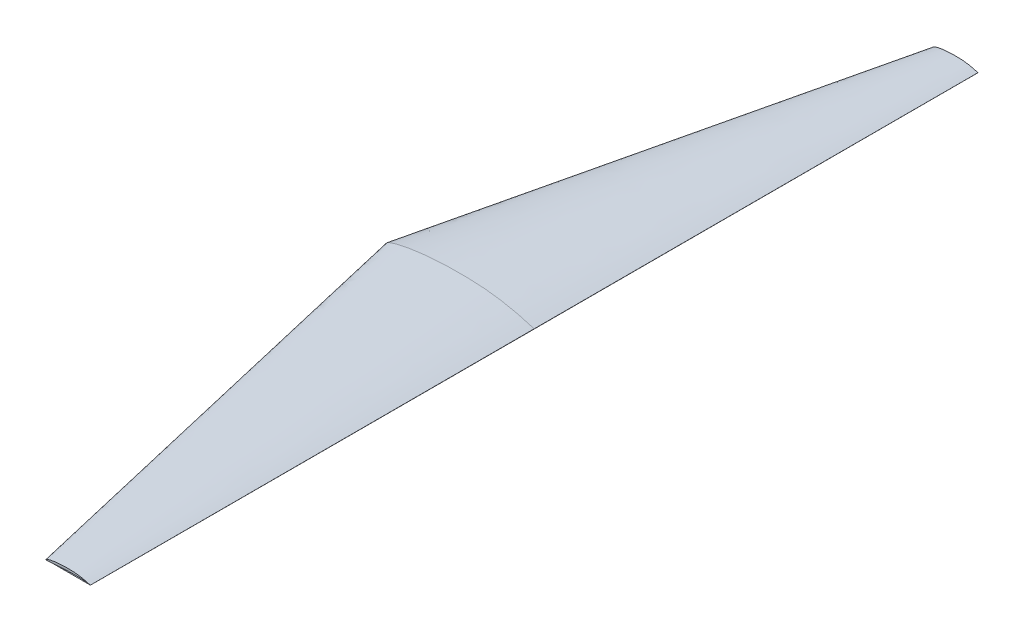
SolidWorks part; units mm, degrees
ref_plane "Front Plane" through (0, 0, 0) normal (0, 0, 1) x (1, 0, 0)
ref_plane "Top Plane" through (0, 0, 0) normal (0, 1, 0) x (1, 0, 0)
ref_plane "Right Plane" through (0, 0, 0) normal (1, 0, 0) x (0, 0, -1)
curve "Curve1"
  spline degree 3 poles (25.4, 0.016, 0) (25.3391, 0.0354, 0) (25.1691, 0.0896, 0) (24.8604, 0.1853, 0) (24.4521, 0.3079, 0) (23.9748, 0.4451, 0) (23.4435, 0.5905, 0) (22.8682, 0.7391, 0) (22.2564, 0.887, 0) (21.6142, 1.0313, 0) (20.9466, 1.1694, 0) (20.258, 1.299, 0) (19.5521, 1.4184, 0) (18.8325, 1.5262, 0) (18.1021, 1.6212, 0) (17.3637, 1.7024, 0) (16.6199, 1.7689, 0) (15.8731, 1.8208, 0) (15.1255, 1.8558, 0) (14.3793, 1.8809, 0) (13.6365, 1.8983, 0) (12.8989, 1.9074, 0) (12.1682, 1.9083, 0) (11.4461, 1.901, 0) (10.7342, 1.8857, 0) (10.0342, 1.8625, 0) (9.3474, 1.8315, 0) (8.6753, 1.7932, 0) (8.0194, 1.7478, 0) (7.3808, 1.6956, 0) (6.761, 1.637, 0) (6.1612, 1.5726, 0) (5.5826, 1.5027, 0) (5.0264, 1.428, 0) (4.4936, 1.3489, 0) (3.9856, 1.2661, 0) (3.5033, 1.1802, 0) (3.0477, 1.0919, 0) (2.6201, 1.0017, 0) (2.2213, 0.9105, 0) (1.8523, 0.8188, 0) (1.5142, 0.7273, 0) (1.2078, 0.6366, 0) (0.9341, 0.5475, 0) (0.694, 0.4605, 0) (0.4882, 0.3763, 0) (0.3176, 0.2954, 0) (0.1826, 0.2183, 0) (0.0836, 0.145, 0) (0.0195, 0.0755, 0) (-0.008, 0.0023, 0) (0.0173, -0.0678, 0) (0.0849, -0.1179, 0) (0.1842, -0.1582, 0) (0.3194, -0.1909, 0) (0.4898, -0.2162, 0) (0.6954, -0.2344, 0) (0.9354, -0.2455, 0) (1.209, -0.2497, 0) (1.5153, -0.2472, 0) (1.8533, -0.2383, 0) (2.2222, -0.2234, 0) (2.621, -0.2028, 0) (3.0486, -0.1768, 0) (3.504, -0.1458, 0) (3.9863, -0.1104, 0) (4.4943, -0.0708, 0) (5.0269, -0.0277, 0) (5.5831, 0.0186, 0) (6.1617, 0.0673, 0) (6.7614, 0.1181, 0) (7.3812, 0.1704, 0) (8.0196, 0.2236, 0) (8.6755, 0.2771, 0) (9.3475, 0.3304, 0) (10.0343, 0.3829, 0) (10.7343, 0.4341, 0) (11.446, 0.4835, 0) (12.1681, 0.5305, 0) (12.8988, 0.5746, 0) (13.6364, 0.6156, 0) (14.3791, 0.6529, 0) (15.1252, 0.6867, 0) (15.8725, 0.7144, 0) (16.6192, 0.7287, 0) (17.363, 0.7312, 0) (18.1013, 0.7217, 0) (18.8317, 0.7006, 0) (19.5514, 0.6682, 0) (20.2572, 0.6255, 0) (20.9458, 0.5732, 0) (21.6134, 0.5125, 0) (22.2557, 0.4449, 0) (22.8675, 0.3721, 0) (23.4429, 0.2962, 0) (23.9743, 0.2197, 0) (24.4517, 0.1457, 0) (24.8601, 0.0785, 0) (25.1689, 0.0253, 0) (25.3391, -0.0051, 0) (25.4, -0.016, 0) knots 0 0 0 0 0.003729 0.010403 0.018841 0.028586 0.039358 0.050957 0.063231 0.076057 0.089334 0.102977 0.11691 0.131071 0.145402 0.159854 0.17438 0.18894 0.203496 0.218017 0.232469 0.246817 0.261029 0.275074 0.288921 0.302543 0.315913 0.329004 0.341791 0.35425 0.366358 0.37809 0.389424 0.400339 0.410813 0.420824 0.430352 0.439376 0.447877 0.455834 0.463229 0.470043 0.476257 0.481856 0.486823 0.491146 0.494814 0.497827 0.500195 0.50197 0.5033 0.504509 0.506013 0.508063 0.510747 0.514093 0.518105 0.522777 0.528099 0.534057 0.540634 0.547815 0.555582 0.563914 0.572793 0.582198 0.592109 0.602502 0.613357 0.624649 0.636356 0.648452 0.660912 0.673711 0.686822 0.700217 0.713868 0.727745 0.741819 0.756057 0.770426 0.784892 0.799419 0.813968 0.828496 0.842964 0.85733 0.871548 0.885567 0.89933 0.912776 0.925832 0.938415 0.950429 0.961757 0.972255 0.981732 0.989922 0.99639 1 1 1 1
sketch "Sketch3" plane through (0, 0, 0) normal (0, 0, 1) x (1, 0, 0)
  line L0 (25.4, 0.016) -> (25.4, -0.016)
  line L1 (0, 0) -> (25.4, 0) construction
  spline S0 degree 3 poles (976.7021, 2844.8263) (53.073, -21.0739) (40.8374, -4.7691) (24.8604, 0.1853) (24.4521, 0.3079) (23.7837, 0.5001) (22.615, 0.8106) (21.3697, 1.0897) (20.0193, 1.3439) (19.0695, 1.4954) (18.1021, 1.6212) (17.3637, 1.7024) (16.6199, 1.7689) (15.8731, 1.8208) (15.1255, 1.8558) (14.3793, 1.8809) (13.6365, 1.8983) (12.658, 1.9103) (11.6898, 1.9063) (10.505, 1.8807) (9.5807, 1.8449) (8.6753, 1.7932) (8.0194, 1.7478) (7.3808, 1.6956) (6.761, 1.637) (6.1612, 1.5726) (5.5826, 1.5027) (5.0264, 1.428) (4.4936, 1.3489) (3.9856, 1.2661) (3.5033, 1.1802) (3.0477, 1.0919) (2.6201, 1.0017) (2.2213, 0.9105) (1.8523, 0.8188) (1.5142, 0.7273) (1.2078, 0.6366) (0.9341, 0.5475) (0.694, 0.4605) (0.4882, 0.3763) (0.3176, 0.2954) (0.1826, 0.2183) (0.0836, 0.145) (0.0195, 0.0755) (-0.008, 0.0023) (0.0173, -0.0678) (0.0849, -0.1179) (0.1842, -0.1582) (0.3194, -0.1909) (0.4898, -0.2162) (0.6954, -0.2344) (0.9354, -0.2455) (1.209, -0.2497) (1.5153, -0.2472) (1.8533, -0.2383) (2.2222, -0.2234) (2.621, -0.2028) (3.0486, -0.1768) (3.504, -0.1458) (3.9863, -0.1104) (4.4943, -0.0708) (5.0269, -0.0277) (5.5831, 0.0186) (6.1617, 0.0673) (6.7614, 0.1181) (7.3812, 0.1704) (8.0196, 0.2236) (8.6755, 0.2771) (9.5809, 0.3489) (10.7458, 0.4363) (11.9305, 0.5161) (12.8988, 0.5746) (13.6364, 0.6156) (14.3791, 0.6529) (15.1252, 0.6867) (15.8725, 0.7144) (16.6192, 0.7287) (17.363, 0.7312) (18.1013, 0.7217) (19.0677, 0.6937) (20.2411, 0.6319) (21.5894, 0.5195) (22.6536, 0.4003) (23.4429, 0.2962) (23.9743, 0.2197) (24.4517, 0.1457) (24.8601, 0.0785) (42.1529, -2.8996) (57.3926, -16.6778) (598.7349, 2944.3395) knots -0.956465 -0.956465 -0.956465 -0.956465 0.003729 0.010403 0.018841 0.028586 0.050957 0.089334 0.102977 0.131071 0.145402 0.159854 0.17438 0.18894 0.203496 0.218017 0.232469 0.246817 0.275074 0.288921 0.315913 0.329004 0.341791 0.35425 0.366358 0.37809 0.389424 0.400339 0.410813 0.420824 0.430352 0.439376 0.447877 0.455834 0.463229 0.470043 0.476257 0.481856 0.486823 0.491146 0.494814 0.497827 0.500195 0.50197 0.5033 0.504509 0.506013 0.508063 0.510747 0.514093 0.518105 0.522777 0.528099 0.534057 0.540634 0.547815 0.555582 0.563914 0.572793 0.582198 0.592109 0.602502 0.613357 0.624649 0.636356 0.648452 0.660912 0.673711 0.686822 0.713868 0.741819 0.756057 0.770426 0.784892 0.799419 0.813968 0.828496 0.842964 0.85733 0.871548 0.89933 0.925832 0.950429 0.961757 0.972255 0.981732 0.989922 0.99639 2.004842 2.004842 2.004842 2.004842 only from (25.4, 0.016) to (25.4, -0.016) construction
  spline S1 degree 3 poles (25.4, 0.016) (25.3391, 0.0354) (25.1691, 0.0896) (24.8604, 0.1853) (24.4521, 0.3079) (23.7837, 0.5001) (22.615, 0.8106) (21.3697, 1.0897) (20.0193, 1.3439) (19.0695, 1.4954) (18.1021, 1.6212) (17.3637, 1.7024) (16.6199, 1.7689) (15.8731, 1.8208) (15.1255, 1.8558) (14.3793, 1.8809) (13.6365, 1.8983) (12.658, 1.9103) (11.6898, 1.9063) (10.505, 1.8807) (9.5807, 1.8449) (8.6753, 1.7932) (8.0194, 1.7478) (7.3808, 1.6956) (6.761, 1.637) (6.1612, 1.5726) (5.5826, 1.5027) (5.0264, 1.428) (4.4936, 1.3489) (3.9856, 1.2661) (3.5033, 1.1802) (3.0477, 1.0919) (2.6201, 1.0017) (2.2213, 0.9105) (1.8523, 0.8188) (1.5142, 0.7273) (1.2078, 0.6366) (0.9341, 0.5475) (0.694, 0.4605) (0.4882, 0.3763) (0.3176, 0.2954) (0.1826, 0.2183) (0.0836, 0.145) (0.0195, 0.0755) (-0.008, 0.0023) (0.0173, -0.0678) (0.0849, -0.1179) (0.1842, -0.1582) (0.3194, -0.1909) (0.4898, -0.2162) (0.6954, -0.2344) (0.9354, -0.2455) (1.209, -0.2497) (1.5153, -0.2472) (1.8533, -0.2383) (2.2222, -0.2234) (2.621, -0.2028) (3.0486, -0.1768) (3.504, -0.1458) (3.9863, -0.1104) (4.4943, -0.0708) (5.0269, -0.0277) (5.5831, 0.0186) (6.1617, 0.0673) (6.7614, 0.1181) (7.3812, 0.1704) (8.0196, 0.2236) (8.6755, 0.2771) (9.5809, 0.3489) (10.7458, 0.4363) (11.9305, 0.5161) (12.8988, 0.5746) (13.6364, 0.6156) (14.3791, 0.6529) (15.1252, 0.6867) (15.8725, 0.7144) (16.6192, 0.7287) (17.363, 0.7312) (18.1013, 0.7217) (19.0677, 0.6937) (20.2411, 0.6319) (21.5894, 0.5195) (22.6536, 0.4003) (23.4429, 0.2962) (23.9743, 0.2197) (24.4517, 0.1457) (24.8601, 0.0785) (25.1689, 0.0253) (25.3391, -0.0051) (25.4, -0.016) knots 0 0 0 0 0.003729 0.010403 0.018841 0.028586 0.050957 0.089334 0.102977 0.131071 0.145402 0.159854 0.17438 0.18894 0.203496 0.218017 0.232469 0.246817 0.275074 0.288921 0.315913 0.329004 0.341791 0.35425 0.366358 0.37809 0.389424 0.400339 0.410813 0.420824 0.430352 0.439376 0.447877 0.455834 0.463229 0.470043 0.476257 0.481856 0.486823 0.491146 0.494814 0.497827 0.500195 0.50197 0.5033 0.504509 0.506013 0.508063 0.510747 0.514093 0.518105 0.522777 0.528099 0.534057 0.540634 0.547815 0.555582 0.563914 0.572793 0.582198 0.592109 0.602502 0.613357 0.624649 0.636356 0.648452 0.660912 0.673711 0.686822 0.713868 0.741819 0.756057 0.770426 0.784892 0.799419 0.813968 0.828496 0.842964 0.85733 0.871548 0.89933 0.925832 0.950429 0.961757 0.972255 0.981732 0.989922 0.99639 1 1 1 1
sketch "Sketch4" plane through (0, 0, 0) normal (0, 0, 1) x (1, 0, 0)
  line L0 (254, 0.16) -> (254, -0.16)
  line L1 (0, 0) -> (254, 0) construction
  line L2 (29.1579, 10.6362) -> (29.1579, -1.8467) construction
  line L3 (63.7675, 15.9532) -> (63.7675, 0.8557) construction
  line L4 (110.6359, 18.9242) -> (110.6359, 4.5682) construction
  line L5 (175.3204, 16.8266) -> (175.3204, 7.2808) construction
  circle A0 centre (73.4807, 9.2885) radius 6.35
  spline S0 degree 3 poles (976.7021, 2844.8263) (53.073, -21.0739) (40.8374, -4.7691) (24.8604, 0.1853) (24.4521, 0.3079) (23.7837, 0.5001) (22.615, 0.8106) (21.3697, 1.0897) (20.0193, 1.3439) (19.0695, 1.4954) (18.1021, 1.6212) (17.3637, 1.7024) (16.6199, 1.7689) (15.8731, 1.8208) (15.1255, 1.8558) (14.3793, 1.8809) (13.6365, 1.8983) (12.658, 1.9103) (11.6898, 1.9063) (10.505, 1.8807) (9.5807, 1.8449) (8.6753, 1.7932) (8.0194, 1.7478) (7.3808, 1.6956) (6.761, 1.637) (6.1612, 1.5726) (5.5826, 1.5027) (5.0264, 1.428) (4.4936, 1.3489) (3.9856, 1.2661) (3.5033, 1.1802) (3.0477, 1.0919) (2.6201, 1.0017) (2.2213, 0.9105) (1.8523, 0.8188) (1.5142, 0.7273) (1.2078, 0.6366) (0.9341, 0.5475) (0.694, 0.4605) (0.4882, 0.3763) (0.3176, 0.2954) (0.1826, 0.2183) (0.0836, 0.145) (0.0195, 0.0755) (-0.008, 0.0023) (0.0173, -0.0678) (0.0849, -0.1179) (0.1842, -0.1582) (0.3194, -0.1909) (0.4898, -0.2162) (0.6954, -0.2344) (0.9354, -0.2455) (1.209, -0.2497) (1.5153, -0.2472) (1.8533, -0.2383) (2.2222, -0.2234) (2.621, -0.2028) (3.0486, -0.1768) (3.504, -0.1458) (3.9863, -0.1104) (4.4943, -0.0708) (5.0269, -0.0277) (5.5831, 0.0186) (6.1617, 0.0673) (6.7614, 0.1181) (7.3812, 0.1704) (8.0196, 0.2236) (8.6755, 0.2771) (9.5809, 0.3489) (10.7458, 0.4363) (11.9305, 0.5161) (12.8988, 0.5746) (13.6364, 0.6156) (14.3791, 0.6529) (15.1252, 0.6867) (15.8725, 0.7144) (16.6192, 0.7287) (17.363, 0.7312) (18.1013, 0.7217) (19.0677, 0.6937) (20.2411, 0.6319) (21.5894, 0.5195) (22.6536, 0.4003) (23.4429, 0.2962) (23.9743, 0.2197) (24.4517, 0.1457) (24.8601, 0.0785) (42.1529, -2.8996) (57.3926, -16.6778) (598.7349, 2944.3395) knots -0.956465 -0.956465 -0.956465 -0.956465 0.003729 0.010403 0.018841 0.028586 0.050957 0.089334 0.102977 0.131071 0.145402 0.159854 0.17438 0.18894 0.203496 0.218017 0.232469 0.246817 0.275074 0.288921 0.315913 0.329004 0.341791 0.35425 0.366358 0.37809 0.389424 0.400339 0.410813 0.420824 0.430352 0.439376 0.447877 0.455834 0.463229 0.470043 0.476257 0.481856 0.486823 0.491146 0.494814 0.497827 0.500195 0.50197 0.5033 0.504509 0.506013 0.508063 0.510747 0.514093 0.518105 0.522777 0.528099 0.534057 0.540634 0.547815 0.555582 0.563914 0.572793 0.582198 0.592109 0.602502 0.613357 0.624649 0.636356 0.648452 0.660912 0.673711 0.686822 0.713868 0.741819 0.756057 0.770426 0.784892 0.799419 0.813968 0.828496 0.842964 0.85733 0.871548 0.89933 0.925832 0.950429 0.961757 0.972255 0.981732 0.989922 0.99639 2.004842 2.004842 2.004842 2.004842 only from (25.4, 0.016) to (25.4, -0.016) construction
  spline S1 degree 3 poles (25.4, 0.016) (25.3391, 0.0354) (25.1691, 0.0896) (24.8604, 0.1853) (24.4521, 0.3079) (23.7837, 0.5001) (22.615, 0.8106) (21.3697, 1.0897) (20.0193, 1.3439) (19.0695, 1.4954) (18.1021, 1.6212) (17.3637, 1.7024) (16.6199, 1.7689) (15.8731, 1.8208) (15.1255, 1.8558) (14.3793, 1.8809) (13.6365, 1.8983) (12.658, 1.9103) (11.6898, 1.9063) (10.505, 1.8807) (9.5807, 1.8449) (8.6753, 1.7932) (8.0194, 1.7478) (7.3808, 1.6956) (6.761, 1.637) (6.1612, 1.5726) (5.5826, 1.5027) (5.0264, 1.428) (4.4936, 1.3489) (3.9856, 1.2661) (3.5033, 1.1802) (3.0477, 1.0919) (2.6201, 1.0017) (2.2213, 0.9105) (1.8523, 0.8188) (1.5142, 0.7273) (1.2078, 0.6366) (0.9341, 0.5475) (0.694, 0.4605) (0.4882, 0.3763) (0.3176, 0.2954) (0.1826, 0.2183) (0.0836, 0.145) (0.0195, 0.0755) (-0.008, 0.0023) (0.0173, -0.0678) (0.0849, -0.1179) (0.1842, -0.1582) (0.3194, -0.1909) (0.4898, -0.2162) (0.6954, -0.2344) (0.9354, -0.2455) (1.209, -0.2497) (1.5153, -0.2472) (1.8533, -0.2383) (2.2222, -0.2234) (2.621, -0.2028) (3.0486, -0.1768) (3.504, -0.1458) (3.9863, -0.1104) (4.4943, -0.0708) (5.0269, -0.0277) (5.5831, 0.0186) (6.1617, 0.0673) (6.7614, 0.1181) (7.3812, 0.1704) (8.0196, 0.2236) (8.6755, 0.2771) (9.5809, 0.3489) (10.7458, 0.4363) (11.9305, 0.5161) (12.8988, 0.5746) (13.6364, 0.6156) (14.3791, 0.6529) (15.1252, 0.6867) (15.8725, 0.7144) (16.6192, 0.7287) (17.363, 0.7312) (18.1013, 0.7217) (19.0677, 0.6937) (20.2411, 0.6319) (21.5894, 0.5195) (22.6536, 0.4003) (23.4429, 0.2962) (23.9743, 0.2197) (24.4517, 0.1457) (24.8601, 0.0785) (25.1689, 0.0253) (25.3391, -0.0051) (25.4, -0.016) knots 0 0 0 0 0.003729 0.010403 0.018841 0.028586 0.050957 0.089334 0.102977 0.131071 0.145402 0.159854 0.17438 0.18894 0.203496 0.218017 0.232469 0.246817 0.275074 0.288921 0.315913 0.329004 0.341791 0.35425 0.366358 0.37809 0.389424 0.400339 0.410813 0.420824 0.430352 0.439376 0.447877 0.455834 0.463229 0.470043 0.476257 0.481856 0.486823 0.491146 0.494814 0.497827 0.500195 0.50197 0.5033 0.504509 0.506013 0.508063 0.510747 0.514093 0.518105 0.522777 0.528099 0.534057 0.540634 0.547815 0.555582 0.563914 0.572793 0.582198 0.592109 0.602502 0.613357 0.624649 0.636356 0.648452 0.660912 0.673711 0.686822 0.713868 0.741819 0.756057 0.770426 0.784892 0.799419 0.813968 0.828496 0.842964 0.85733 0.871548 0.89933 0.925832 0.950429 0.961757 0.972255 0.981732 0.989922 0.99639 1 1 1 1 construction
  spline S2 degree 3 poles (254, 0.16) (253.3906, 0.3542) (251.6907, 0.8958) (248.6043, 1.8529) (244.5211, 3.0787) (237.8365, 5.0012) (226.1504, 8.106) (213.6966, 10.8972) (200.1927, 13.4392) (190.6948, 14.9542) (181.0206, 16.2119) (173.6368, 17.0237) (166.1991, 17.6893) (158.7314, 18.2077) (151.255, 18.5582) (143.7934, 18.8085) (136.3654, 18.9829) (126.5803, 19.1033) (116.8978, 19.0625) (105.0498, 18.8074) (95.8066, 18.4485) (86.7534, 17.9322) (80.1938, 17.4777) (73.8085, 16.9557) (67.6104, 16.3701) (61.6122, 15.7256) (55.826, 15.0269) (50.2635, 14.2795) (44.9364, 13.4889) (39.8557, 12.6611) (35.0325, 11.8022) (30.4774, 10.9189) (26.2007, 10.0175) (22.2126, 9.1048) (18.5231, 8.1876) (15.1417, 7.2725) (12.078, 6.3662) (9.341, 5.4751) (6.9396, 4.6054) (4.882, 3.7633) (3.1758, 2.9538) (1.8262, 2.1835) (0.8359, 1.45) (0.195, 0.7552) (-0.0804, 0.0232) (0.1728, -0.6777) (0.8492, -1.1792) (1.8421, -1.5824) (3.1937, -1.9088) (4.898, -2.1625) (6.9544, -2.3441) (9.3544, -2.4548) (12.0902, -2.4967) (15.153, -2.472) (18.5335, -2.3835) (22.2222, -2.2344) (26.2096, -2.0279) (30.4856, -1.7679) (35.0401, -1.4583) (39.8627, -1.1036) (44.9428, -0.7081) (50.2693, -0.2767) (55.8311, 0.1856) (61.6167, 0.6734) (67.6143, 1.1815) (73.8117, 1.7043) (80.1964, 2.236) (86.7554, 2.7712) (95.8093, 3.4893) (107.4576, 4.3628) (119.3051, 5.1609) (128.9876, 5.7464) (136.3636, 6.1563) (143.7914, 6.5288) (151.2515, 6.8672) (158.7251, 7.1439) (166.1924, 7.2865) (173.6296, 7.3121) (181.0132, 7.217) (190.6768, 6.9373) (202.4106, 6.3191) (215.8943, 5.1954) (226.5356, 4.0034) (234.4293, 2.9619) (239.7432, 2.1966) (244.5169, 1.4571) (248.6014, 0.7846) (251.6891, 0.2529) (253.3905, -0.0511) (254, -0.16) knots 0 0 0 0 0.003729 0.010403 0.018841 0.028586 0.050957 0.089334 0.102977 0.131071 0.145402 0.159854 0.17438 0.18894 0.203496 0.218017 0.232469 0.246817 0.275074 0.288921 0.315913 0.329004 0.341791 0.35425 0.366358 0.37809 0.389424 0.400339 0.410813 0.420824 0.430352 0.439376 0.447877 0.455834 0.463229 0.470043 0.476257 0.481856 0.486823 0.491146 0.494814 0.497827 0.500195 0.50197 0.5033 0.504509 0.506013 0.508063 0.510747 0.514093 0.518105 0.522777 0.528099 0.534057 0.540634 0.547815 0.555582 0.563914 0.572793 0.582198 0.592109 0.602502 0.613357 0.624649 0.636356 0.648452 0.660912 0.673711 0.686822 0.713868 0.741819 0.756057 0.770426 0.784892 0.799419 0.813968 0.828496 0.842964 0.85733 0.871548 0.89933 0.925832 0.950429 0.961757 0.972255 0.981732 0.989922 0.99639 1 1 1 1
  spline S3 degree 3 poles (0, 0) (21.1494, 3.5172) (57.9667, 8.4117) (142.9544, 14.3579) (207.0946, 13.0377) (254, 0) knots 0 0 0 0 0.251677 0.43551 1 1 1 1 construction
  dimension "D3" = 12.7
  dimension "D1" = 254
  dimension "D2" = 0.32
ref_plane "Plane1" through (0, 0, 762) normal (0, 0, 1) x (1, 0, 0)
sketch "Sketch5" plane through (0, 0, 762) normal (0, 0, 1) x (1, 0, 0)
  line L0 (254, 0.016) -> (254, -0.016)
  line L1 (228.6, 0) -> (254, 0) construction
  line L2 (241.3, 0) -> (241.3, 0.5624) construction
  line L3 (254, 0.048) -> (254, -0.048)
  spline S0 degree 3 poles (254, 0.016) (253.9391, 0.0354) (253.7691, 0.0896) (253.4604, 0.1853) (253.0521, 0.3079) (252.3837, 0.5001) (251.215, 0.8106) (249.9697, 1.0897) (248.6193, 1.3439) (247.6695, 1.4954) (246.7021, 1.6212) (245.9637, 1.7024) (245.2199, 1.7689) (244.4731, 1.8208) (243.7255, 1.8558) (242.9793, 1.8809) (242.2365, 1.8983) (241.258, 1.9103) (240.2898, 1.9063) (239.105, 1.8807) (238.1807, 1.8449) (237.2753, 1.7932) (236.6194, 1.7478) (235.9808, 1.6956) (235.361, 1.637) (234.7612, 1.5726) (234.1826, 1.5027) (233.6264, 1.428) (233.0936, 1.3489) (232.5856, 1.2661) (232.1033, 1.1802) (231.6477, 1.0919) (231.2201, 1.0017) (230.8213, 0.9105) (230.4523, 0.8188) (230.1142, 0.7273) (229.8078, 0.6366) (229.5341, 0.5475) (229.294, 0.4605) (229.0882, 0.3763) (228.9176, 0.2954) (228.7826, 0.2183) (228.6836, 0.145) (228.6195, 0.0755) (228.592, 0.0023) (228.6173, -0.0678) (228.6849, -0.1179) (228.7842, -0.1582) (228.9194, -0.1909) (229.0898, -0.2162) (229.2954, -0.2344) (229.5354, -0.2455) (229.809, -0.2497) (230.1153, -0.2472) (230.4533, -0.2383) (230.8222, -0.2234) (231.221, -0.2028) (231.6486, -0.1768) (232.104, -0.1458) (232.5863, -0.1104) (233.0943, -0.0708) (233.6269, -0.0277) (234.1831, 0.0186) (234.7617, 0.0673) (235.3614, 0.1181) (235.9812, 0.1704) (236.6196, 0.2236) (237.2755, 0.2771) (238.1809, 0.3489) (239.3458, 0.4363) (240.5305, 0.5161) (241.4988, 0.5746) (242.2364, 0.6156) (242.9791, 0.6529) (243.7252, 0.6867) (244.4725, 0.7144) (245.2192, 0.7287) (245.963, 0.7312) (246.7013, 0.7217) (247.6677, 0.6937) (248.8411, 0.6319) (250.1894, 0.5195) (251.2536, 0.4003) (252.0429, 0.2962) (252.5743, 0.2197) (253.0517, 0.1457) (253.4601, 0.0785) (253.7689, 0.0253) (253.9391, -0.0051) (254, -0.016) knots 0 0 0 0 0.003729 0.010403 0.018841 0.028586 0.050957 0.089334 0.102977 0.131071 0.145402 0.159854 0.17438 0.18894 0.203496 0.218017 0.232469 0.246817 0.275074 0.288921 0.315913 0.329004 0.341791 0.35425 0.366358 0.37809 0.389424 0.400339 0.410813 0.420824 0.430352 0.439376 0.447877 0.455834 0.463229 0.470043 0.476257 0.481856 0.486823 0.491146 0.494814 0.497827 0.500195 0.50197 0.5033 0.504509 0.506013 0.508063 0.510747 0.514093 0.518105 0.522777 0.528099 0.534057 0.540634 0.547815 0.555582 0.563914 0.572793 0.582198 0.592109 0.602502 0.613357 0.624649 0.636356 0.648452 0.660912 0.673711 0.686822 0.713868 0.741819 0.756057 0.770426 0.784892 0.799419 0.813968 0.828496 0.842964 0.85733 0.871548 0.89933 0.925832 0.950429 0.961757 0.972255 0.981732 0.989922 0.99639 1 1 1 1 construction
  spline S1 degree 3 poles (254, 0.048) (253.8172, 0.1063) (253.3072, 0.2687) (252.3813, 0.5559) (251.1563, 0.9236) (249.151, 1.5003) (245.6451, 2.4318) (241.909, 3.2692) (237.8578, 4.0318) (235.0084, 4.4863) (232.1062, 4.8636) (229.891, 5.1071) (227.6597, 5.3068) (225.4194, 5.4623) (223.1765, 5.5675) (220.938, 5.6426) (218.7096, 5.6949) (215.7741, 5.731) (212.8693, 5.7188) (209.3149, 5.6422) (206.542, 5.5346) (203.826, 5.3796) (201.8581, 5.2433) (199.9425, 5.0867) (198.0831, 4.911) (196.2837, 4.7177) (194.5478, 4.5081) (192.8791, 4.2839) (191.2809, 4.0467) (189.7567, 3.7983) (188.3098, 3.5407) (186.9432, 3.2757) (185.6602, 3.0052) (184.4638, 2.7314) (183.3569, 2.4563) (182.3425, 2.1818) (181.4234, 1.9099) (180.6023, 1.6425) (179.8819, 1.3816) (179.2646, 1.129) (178.7527, 0.8861) (178.3479, 0.655) (178.0508, 0.435) (177.8585, 0.2266) (177.7759, 0.007) (177.8518, -0.2033) (178.0548, -0.3538) (178.3526, -0.4747) (178.7581, -0.5726) (179.2694, -0.6487) (179.8863, -0.7032) (180.6063, -0.7364) (181.4271, -0.749) (182.3459, -0.7416) (183.36, -0.715) (184.4667, -0.6703) (185.6629, -0.6084) (186.9457, -0.5304) (188.312, -0.4375) (189.7588, -0.3311) (191.2828, -0.2124) (192.8808, -0.083) (194.5493, 0.0557) (196.285, 0.202) (198.0843, 0.3544) (199.9435, 0.5113) (201.8589, 0.6708) (203.8266, 0.8314) (206.5428, 1.0468) (210.0373, 1.3088) (213.5915, 1.5483) (216.4963, 1.7239) (218.7091, 1.8469) (220.9374, 1.9586) (223.1755, 2.0602) (225.4175, 2.1432) (227.6577, 2.186) (229.8889, 2.1936) (232.1039, 2.1651) (235.003, 2.0812) (238.5232, 1.8957) (242.5683, 1.5586) (245.7607, 1.201) (248.1288, 0.8886) (249.723, 0.659) (251.1551, 0.4371) (252.3804, 0.2354) (253.3067, 0.0759) (253.8172, -0.0153) (254, -0.048) knots 0 0 0 0 0.003729 0.010403 0.018841 0.028586 0.050957 0.089334 0.102977 0.131071 0.145402 0.159854 0.17438 0.18894 0.203496 0.218017 0.232469 0.246817 0.275074 0.288921 0.315913 0.329004 0.341791 0.35425 0.366358 0.37809 0.389424 0.400339 0.410813 0.420824 0.430352 0.439376 0.447877 0.455834 0.463229 0.470043 0.476257 0.481856 0.486823 0.491146 0.494814 0.497827 0.500195 0.50197 0.5033 0.504509 0.506013 0.508063 0.510747 0.514093 0.518105 0.522777 0.528099 0.534057 0.540634 0.547815 0.555582 0.563914 0.572793 0.582198 0.592109 0.602502 0.613357 0.624649 0.636356 0.648452 0.660912 0.673711 0.686822 0.713868 0.741819 0.756057 0.770426 0.784892 0.799419 0.813968 0.828496 0.842964 0.85733 0.871548 0.89933 0.925832 0.950429 0.961757 0.972255 0.981732 0.989922 0.99639 1 1 1 1
  dimension "D1" = 25.4
  dimension "D2" = 0.032
  dimension "D3" = 0.5624
loft "Loft2" add section "Sketch4" section "Sketch5"
mirror "Mirror1" about plane through (0.8571, 1.4236, 0) normal (0, 0, -1) of "Loft2"
sketch "Sketch6" plane through (0, 0, 0) normal (0, 1, 0) x (1, 0, 0)
  line L0 (177.8, 762) -> (254, 762)
  line L1 (177.8, 762) -> (254, 762)
  line L2 (254, 762) -> (254, 0)
  line L3 (254, 762) -> (254, 0)
  line L4 (254, 0) -> (254, -762)
  line L5 (254, 0) -> (254, -762)
  line L6 (254, -762) -> (177.8, -762)
  line L7 (254, -762) -> (177.8, -762)
  line L8 (177.8, -762) -> (-0.0001, 0)
  line L9 (177.8, -762) -> (-0.0001, 0)
  line L10 (-0.0001, 0) -> (177.8, 762)
  line L11 (-0.0001, 0) -> (177.8, 762)
surface "Surface-Plane1" sketch "Sketch6"
